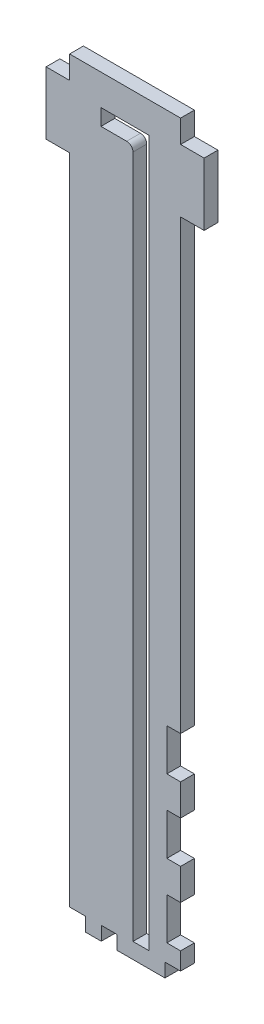
SolidWorks part; units mm, degrees
material "Acrylic (Medium-high impact)"
ref_plane "Front" through (0, 0, 0) normal (0, 0, 1) x (1, 0, 0)
ref_plane "Top" through (0, 0, 0) normal (0, 1, 0) x (1, 0, 0)
ref_plane "Right" through (0, 0, 0) normal (1, 0, 0) x (0, 0, -1)
sketch "Sketch1" plane through (0, 0, 0) normal (0, 0, 1) x (1, 0, 0)
  line L0 (0, 143.002) -> (0, -143.002) construction
  line L1 (-3.302, 133.858) -> (-3.302, -143.002)
  line L2 (-3.302, -143.002) -> (3.302, -143.002)
  line L3 (3.302, 143.002) -> (3.302, -143.002)
  line L4 (3.302, 143.002) -> (-16.256, 143.002)
  line L5 (-5.842, 136.398) -> (-16.256, 136.398)
  line L6 (-16.256, 143.002) -> (-16.256, 136.398)
  line L8 (-28.956, 155.448) -> (16.002, 155.448)
  line L9 (-28.956, 155.448) -> (-28.956, -149.352)
  line L10 (-28.956, -149.352) -> (16.002, -149.352)
  line L11 (16.002, 155.448) -> (16.002, -149.352)
  arc A0 (-3.302, 133.858) -> (-5.842, 136.398) centre (-5.842, 133.858) ccw
  point P2 (0, -143.002)
  point P11 (0, 0)
  dimension "D5" = 2.54
  dimension "D1" = 6.604
  dimension "D2" = 12.954
  dimension "D3" = 6.604
  dimension "D4" = 286.004
  dimension "D6" = 304.8
  dimension "D7" = 6.35
  dimension "D8" = 12.7
  dimension "D9" = 12.7
extrude "Boss-Extrude1" add sketch "Sketch1" along normal blind 5.588
sketch "Sketch2" plane through (16.002, 0, 0) normal (1, 0, 0) x (0, 0, -1)
  line L0 (-5.588, -149.352) -> (-5.588, 155.448) construction
  line L1 (-5.588, -47.752) -> (228.6, -47.752)
  line L2 (-5.588, -47.752) -> (-5.588, -149.352)
  line L3 (-5.588, -149.352) -> (228.6, -149.352)
  line L4 (228.6, -47.752) -> (228.6, -149.352)
  line L5 (14.4, -101.092) -> (14.4, -96.012)
  line L6 (36.4, -96.012) -> (36.4, -101.092)
  line L7 (8.4, -116.592) -> (8.4, -111.512)
  line L8 (11.4, -116.592) -> (11.4, -111.512)
  line L9 (8.4, -85.592) -> (8.4, -80.512)
  line L10 (11.4, -85.592) -> (11.4, -80.512)
  line L11 (25.4, -96.012) -> (25.4, -101.092) construction
  line L12 (42.4, -116.592) -> (42.4, -111.512)
  line L13 (39.4, -116.592) -> (39.4, -111.512)
  line L14 (39.4, -85.592) -> (39.4, -80.512)
  line L15 (42.4, -85.592) -> (42.4, -80.512)
  line L16 (0, -149.352) -> (0, 155.448) construction
  line L17 (225.425, -60.452) -> (225.425, -77.3853) construction
  line L18 (228.6, -47.752) -> (222.25, -47.752)
  line L19 (228.6, -47.752) -> (228.6, -60.452)
  line L20 (228.6, -60.452) -> (222.25, -60.452)
  line L21 (222.25, -47.752) -> (222.25, -60.452)
  line L22 (228.6, -107.0187) -> (222.25, -107.0187)
  line L23 (228.6, -107.0187) -> (228.6, -119.7187)
  line L24 (228.6, -119.7187) -> (222.25, -119.7187)
  line L25 (222.25, -107.0187) -> (222.25, -119.7187)
  line L26 (228.6, -136.652) -> (222.25, -136.652)
  line L27 (228.6, -136.652) -> (228.6, -149.352)
  line L28 (228.6, -149.352) -> (222.25, -149.352)
  line L29 (222.25, -136.652) -> (222.25, -149.352)
  line L30 (228.6, -77.3853) -> (222.25, -77.3853)
  line L31 (228.6, -77.3853) -> (228.6, -90.0853)
  line L32 (228.6, -90.0853) -> (222.25, -90.0853)
  line L33 (222.25, -77.3853) -> (222.25, -90.0853)
  line L34 (225.425, -90.0853) -> (225.425, -107.0187) construction
  line L35 (225.425, -119.7187) -> (225.425, -136.652) construction
  arc A0 (14.4, -101.092) -> (36.4, -101.092) centre (25.4, -101.092) ccw
  arc A1 (36.4, -96.012) -> (14.4, -96.012) centre (25.4, -96.012) ccw
  arc A2 (8.4, -116.592) -> (11.4, -116.592) centre (9.9, -116.592) ccw
  arc A3 (11.4, -111.512) -> (8.4, -111.512) centre (9.9, -111.512) ccw
  arc A4 (8.4, -85.592) -> (11.4, -85.592) centre (9.9, -85.592) ccw
  arc A5 (11.4, -80.512) -> (8.4, -80.512) centre (9.9, -80.512) ccw
  arc A6 (42.4, -116.592) -> (39.4, -116.592) centre (40.9, -116.592) cw
  arc A7 (39.4, -111.512) -> (42.4, -111.512) centre (40.9, -111.512) cw
  arc A8 (42.4, -85.592) -> (39.4, -85.592) centre (40.9, -85.592) cw
  arc A9 (39.4, -80.512) -> (42.4, -80.512) centre (40.9, -80.512) cw
  point P44 (25.4, -98.552)
  point P47 (-5.588, -98.552)
  line M17 (0, -149.352) -> (0, 155.448)
  line M19 (-5.588, 155.448) -> (-5.588, -149.352)
  line M20 (-5.588, -149.352) -> (0, -149.352)
  dimension "D1" = 22
  dimension "D6" = 1.5
  dimension "D10" = 1.5
  dimension "D2" = 5.08
  dimension "D3" = 5.08
  dimension "D4" = 15.5
  dimension "D5" = 15.5
  dimension "D7" = 15.5
  dimension "D8" = 15.5
  dimension "D9" = 5.08
  dimension "D11" = 25.4
  dimension "D12" = 50.8
  dimension "D13" = 203.2
  dimension "D14" = 12.7
  dimension "D15" = 6.35
extrude "Boss-Extrude2" add sketch "Sketch2" against normal blind 5.588 contours L33 L30 L4 L20 L21 L1 L3 L29 L26 L24 L25 L22 L32 A5 L10 A4 L9 A3 L8 A2 L7 A1 L6 A0 L5 L13 A7 L12 A6 L14 A9 L15 A8 M17 | L1 M19 M20 M17
sketch "Sketch3" plane through (10.414, 0, 0) normal (-1, 0, 0) x (0, 0, 1)
  line L0 (-222.25, -136.652) -> (-222.25, -149.352) construction
  line L1 (-222.25, -143.764) -> (0, -143.764)
  line L2 (-222.25, -143.764) -> (-222.25, -149.352)
  line L3 (-222.25, -149.352) -> (0, -149.352)
  line L4 (0, -143.764) -> (0, -149.352)
  dimension "D1" = 5.588
extrude "Boss-Extrude3" add sketch "Sketch3" along normal up to surface (39.37 mm away) up to face at (-28.956, 3.048, 2.794)
sketch "Sketch4" plane through (0, -149.352, 0) normal (0, -1, 0) x (1, 0, 0)
  line L0 (9.652, -21.3042) -> (9.652, -34.0042)
  line L1 (16.002, 5.588) -> (9.652, 5.588)
  line L2 (16.002, 5.588) -> (16.002, -7.112)
  line L3 (16.002, -7.112) -> (9.652, -7.112)
  line L4 (9.652, 5.588) -> (9.652, -7.112)
  line L5 (16.002, -21.3042) -> (9.652, -21.3042)
  line L6 (16.002, -21.3042) -> (16.002, -34.0042)
  line L7 (16.002, -34.0042) -> (9.652, -34.0042)
  line L8 (9.652, -48.1965) -> (9.652, -60.8965)
  line L9 (16.002, -48.1965) -> (9.652, -48.1965)
  line L10 (16.002, -48.1965) -> (16.002, -60.8965)
  line L11 (16.002, -60.8965) -> (9.652, -60.8965)
  line L12 (9.652, -75.0887) -> (9.652, -87.7887)
  line L13 (16.002, -75.0887) -> (9.652, -75.0887)
  line L14 (16.002, -75.0887) -> (16.002, -87.7887)
  line L15 (16.002, -87.7887) -> (9.652, -87.7887)
  line L16 (9.652, -101.981) -> (9.652, -114.681)
  line L17 (16.002, -101.981) -> (9.652, -101.981)
  line L18 (16.002, -101.981) -> (16.002, -114.681)
  line L19 (16.002, -114.681) -> (9.652, -114.681)
  line L20 (9.652, -128.8732) -> (9.652, -141.5733)
  line L21 (16.002, -128.8732) -> (9.652, -128.8732)
  line L22 (16.002, -128.8732) -> (16.002, -141.5733)
  line L23 (16.002, -141.5733) -> (9.652, -141.5733)
  line L24 (9.652, -155.7655) -> (9.652, -168.4655)
  line L25 (16.002, -155.7655) -> (9.652, -155.7655)
  line L26 (16.002, -155.7655) -> (16.002, -168.4655)
  line L27 (16.002, -168.4655) -> (9.652, -168.4655)
  line L28 (9.652, -182.6577) -> (9.652, -195.3578)
  line L29 (16.002, -182.6577) -> (9.652, -182.6577)
  line L30 (16.002, -182.6577) -> (16.002, -195.3578)
  line L31 (16.002, -195.3578) -> (9.652, -195.3578)
  line L32 (9.652, -209.55) -> (9.652, -222.25)
  line L33 (16.002, -209.55) -> (9.652, -209.55)
  line L34 (16.002, -209.55) -> (16.002, -222.25)
  line L35 (16.002, -222.25) -> (9.652, -222.25)
  line L36 (-6.477, 5.588) -> (-6.477, -222.25) construction
  line L37 (-28.956, 5.588) -> (16.002, 5.588) construction
  line L38 (-28.956, -222.25) -> (16.002, -222.25) construction
  line L39 (-22.606, 5.588) -> (-22.606, -222.25)
  line L40 (16.002, 5.588) -> (9.652, 5.588)
  line L41 (16.002, 5.588) -> (16.002, -222.25)
  line L42 (16.002, -222.25) -> (9.652, -222.25)
  line L43 (9.652, 5.588) -> (9.652, -222.25)
  line L44 (-28.956, -222.25) -> (-22.606, -222.25)
  line L45 (-28.956, 5.588) -> (-28.956, -222.25)
  line L46 (-28.956, 5.588) -> (-22.606, 5.588)
  line L47 (-28.956, -222.25) -> (-22.606, -222.25)
  line L48 (-28.956, -209.55) -> (-28.956, -222.25)
  line L49 (-28.956, -209.55) -> (-22.606, -209.55)
  line L50 (-22.606, -209.55) -> (-22.606, -222.25)
  line L51 (-28.956, -195.3578) -> (-22.606, -195.3578)
  line L52 (-28.956, -182.6577) -> (-28.956, -195.3578)
  line L53 (-28.956, -182.6577) -> (-22.606, -182.6577)
  line L54 (-22.606, -182.6577) -> (-22.606, -195.3578)
  line L55 (-28.956, -168.4655) -> (-22.606, -168.4655)
  line L56 (-28.956, -155.7655) -> (-28.956, -168.4655)
  line L57 (-28.956, -155.7655) -> (-22.606, -155.7655)
  line L58 (-22.606, -155.7655) -> (-22.606, -168.4655)
  line L59 (-28.956, -141.5733) -> (-22.606, -141.5733)
  line L60 (-28.956, -128.8732) -> (-28.956, -141.5733)
  line L61 (-28.956, -128.8732) -> (-22.606, -128.8732)
  line L62 (-22.606, -128.8732) -> (-22.606, -141.5733)
  line L63 (-28.956, -114.681) -> (-22.606, -114.681)
  line L64 (-28.956, -101.981) -> (-28.956, -114.681)
  line L65 (-28.956, -101.981) -> (-22.606, -101.981)
  line L66 (-22.606, -101.981) -> (-22.606, -114.681)
  line L67 (-28.956, -87.7887) -> (-22.606, -87.7887)
  line L68 (-28.956, -75.0887) -> (-28.956, -87.7887)
  line L69 (-28.956, -75.0887) -> (-22.606, -75.0887)
  line L70 (-22.606, -75.0887) -> (-22.606, -87.7887)
  line L71 (-28.956, -60.8965) -> (-22.606, -60.8965)
  line L72 (-28.956, -48.1965) -> (-28.956, -60.8965)
  line L73 (-28.956, -48.1965) -> (-22.606, -48.1965)
  line L74 (-22.606, -48.1965) -> (-22.606, -60.8965)
  line L75 (-28.956, -34.0042) -> (-22.606, -34.0042)
  line L76 (-28.956, -21.3042) -> (-28.956, -34.0042)
  line L77 (-28.956, -21.3042) -> (-22.606, -21.3042)
  line L78 (-22.606, 5.588) -> (-22.606, -7.112)
  line L79 (-28.956, -7.112) -> (-22.606, -7.112)
  line L80 (-28.956, 5.588) -> (-28.956, -7.112)
  line L81 (-28.956, 5.588) -> (-22.606, 5.588)
  line L82 (-22.606, -21.3042) -> (-22.606, -34.0042)
  line L83 (-16.129, 2.794) -> (-22.606, 2.794) construction
  line L85 (-28.956, 5.588) -> (-22.606, 5.588)
  line L86 (-28.956, 5.588) -> (-28.956, 0)
  line L87 (-28.956, 0) -> (-22.606, 0)
  line L88 (-22.606, 5.588) -> (-22.606, 0)
  line L92 (9.652, 5.588) -> (9.652, 0)
  line L93 (9.652, 5.588) -> (16.002, 5.588)
  line L94 (16.002, 5.588) -> (16.002, 0)
  line L95 (9.652, 0) -> (16.002, 0)
  line L96 (-28.956, 5.588) -> (16.002, 5.588)
  line L97 (-28.956, 5.588) -> (-28.956, 0)
  line L98 (-28.956, 0) -> (16.002, 0)
  line L99 (16.002, 5.588) -> (16.002, 0)
  line L100 (-9.652, 5.588) -> (-9.652, 0) [skipped]
  line L101 (-9.652, 0) -> (-3.302, 0) [skipped]
  line L102 (-3.302, 5.588) -> (-3.302, 0) [skipped]
  line L103 (-9.652, 5.588) -> (-3.302, 5.588) [skipped]
  line L104 (-9.779, 0) -> (-16.129, 0)
  line L105 (-9.779, 0) -> (-9.779, 5.588)
  line L106 (-9.779, 5.588) -> (-16.129, 5.588)
  line L107 (-16.129, 0) -> (-16.129, 5.588)
  line L108 (-9.779, 2.794) -> (-3.302, 2.794) construction
  line L109 (-3.302, 5.588) -> (-3.302, 0) construction
  line M39 (16.002, 5.588) -> (-28.956, 5.588)
  line M40 (-28.956, 5.588) -> (-28.956, -222.25)
  dimension "D1" = 6.35
  dimension "D2" = 12.7
  dimension "D4" = 5.588
  dimension "D5" = 6.35
  dimension "D7" = 6.35
  dimension "D3" = 9
  dimension "D6" = 3
sketch "Sketch6" plane through (0, 0, 5.588) normal (0, 0, 1) x (1, 0, 0)
  line L1 (16.002, -60.452) -> (10.414, -60.452)
  line L2 (16.002, -60.452) -> (16.002, -77.3853)
  line L3 (16.002, -77.3853) -> (10.414, -77.3853)
  line L4 (10.414, -60.452) -> (10.414, -77.3853)
  line L5 (16.002, -90.0853) -> (10.414, -90.0853)
  line L6 (16.002, -90.0853) -> (16.002, -107.0187)
  line L7 (16.002, -107.0187) -> (10.414, -107.0187)
  line L8 (10.414, -90.0853) -> (10.414, -107.0187)
  line L9 (16.002, -119.7187) -> (10.414, -119.7187)
  line L10 (16.002, -119.7187) -> (16.002, -136.652)
  line L11 (16.002, -136.652) -> (10.414, -136.652)
  line L12 (10.414, -119.7187) -> (10.414, -136.652)
sketch "Sketch7" plane through (16.002, 0, 0) normal (1, 0, 0) x (0, 0, -1)
  line L0 (0, -47.752) -> (0, 155.448) construction
  line L1 (0, -8.6302) -> (327.0227, -8.6302)
  line L2 (0, -8.6302) -> (0, -288.0659)
  line L3 (0, -288.0659) -> (327.0227, -288.0659)
  line L4 (327.0227, -8.6302) -> (327.0227, -288.0659)
extrude "Cut-Extrude1" cut sketch "Sketch7" against normal through all
extrude "Cut-Extrude2" cut sketch "Sketch4" against normal blind 5.588 contours L107 L98 L105 L96 | L4 L95 L41 M39 | L87 L39 M40 M39 | L20 L23 L22 L21 | L10 L11 L8 L9 | L24 L27 L26 L25
extrude "Cut-Extrude3" cut sketch "Sketch6" against normal through all
sketch "Sketch8" plane through (0, 0, 5.588) normal (0, 0, 1) x (1, 0, 0)
  line L0 (-28.956, 155.448) -> (-28.956, -143.764) construction
  line L1 (-28.956, 146.177) -> (-38.481, 146.177)
  line L2 (-28.956, 146.177) -> (-28.956, 120.777)
  line L3 (-28.956, 120.777) -> (-38.481, 120.777)
  line L4 (-38.481, 146.177) -> (-38.481, 120.777)
  line L5 (16.002, -60.452) -> (16.002, 155.448) construction
  line L6 (16.002, 146.177) -> (25.527, 146.177)
  line L7 (16.002, 146.177) -> (16.002, 120.777)
  line L8 (16.002, 120.777) -> (25.527, 120.777)
  line L9 (25.527, 146.177) -> (25.527, 120.777)
  line L12 (3.302, 143.002) -> (-16.256, 143.002) construction
  point P12 (38.2014, 133.1476)
  dimension "D1" = 9.525
  dimension "D2" = 25.4
  dimension "D3" = 3.175
extrude "Boss-Extrude4" add sketch "Sketch8" against normal up to surface (5.588 mm away) up to face at (-5.404, 58.1686, 0)
